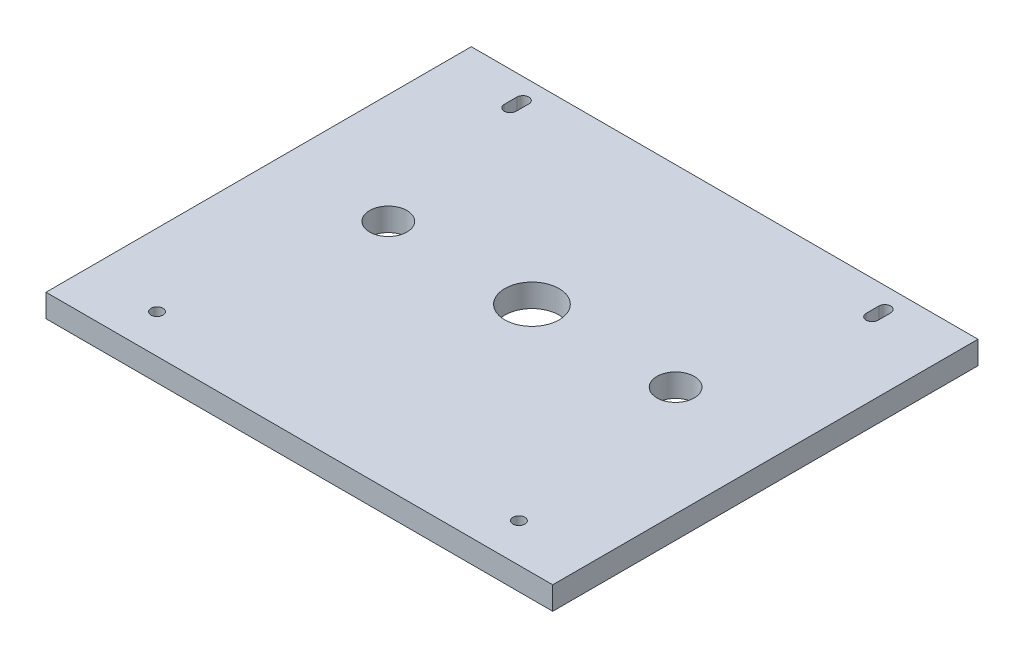
SolidWorks part; units mm, degrees
ref_plane "Front Plane" through (0, 0, 0) normal (0, 0, 1) x (1, 0, 0)
ref_plane "Top Plane" through (0, 0, 0) normal (0, 1, 0) x (1, 0, 0)
ref_plane "Right Plane" through (0, 0, 0) normal (1, 0, 0) x (0, 0, -1)
sketch "Sketch1" plane through (0, 0, 0) normal (0, 1, 0) x (1, 0, 0)
  line L1 (0, 0) -> (140, 0)
  line L2 (0, 0) -> (0, 117.505)
  line L3 (0, 117.505) -> (140, 117.505)
  line L4 (140, 0) -> (140, 117.505)
  dimension "D1" = 117.505
  dimension "D2" = 140
extrude "Boss-Extrude1" add sketch "Sketch1" along normal blind 6.35
sketch "Sketch2" plane through (0, 6.35, 0) normal (0, 1, 0) x (1, 0, 0)
  line L1 (0, 117.505) -> (0, 0) construction
  line L2 (140, 0) -> (140, 117.505) construction
  line L3 (70, 117.505) -> (70, 0) construction
  line L4 (140, 117.505) -> (0, 117.505) construction
  line L5 (0, 0) -> (140, 0) construction
  line L6 (0, 10.675) -> (140, 10.675) construction
  line L7 (0, 110.005) -> (140, 110.005) construction
  line L8 (120, 108.255) -> (120, 111.755) construction
  line L11 (20, 108.255) -> (20, 111.755) construction
  line L12 (18.35, 108.255) -> (18.35, 111.755)
  line L13 (21.65, 108.255) -> (21.65, 111.755)
  line L14 (121.65, 108.255) -> (121.65, 111.755)
  line L17 (118.35, 108.255) -> (118.35, 111.755)
  circle A0 centre (20, 10.675) radius 1.65
  arc A6 (18.35, 108.255) -> (21.65, 108.255) centre (20, 108.255) ccw
  arc A7 (21.65, 111.755) -> (18.35, 111.755) centre (20, 111.755) ccw
  circle A12 centre (70, 64.265) radius 7.5
  circle A15 centre (30.3125, 64.265) radius 5.16
  circle A16 centre (120, 10.675) radius 1.65
  circle A17 centre (109.6875, 64.265) radius 5.16
  arc A18 (121.65, 108.255) -> (118.35, 108.255) centre (120, 108.255) cw
  arc A19 (118.35, 111.755) -> (121.65, 111.755) centre (120, 111.755) cw
  point P26 (120, 110.005)
  point P33 (20, 110.005)
  dimension "D5" = 3.3
  dimension "D10" = 15
  dimension "D8" = 10.32
  dimension "D2" = 45.74
  dimension "D3" = 50
  dimension "D4" = 50
  dimension "D6" = 3.3
  dimension "D7" = 3.5
  dimension "D9" = 39.6875
  dimension "D11" = 10.675
  dimension "D13" = 53.59
extrude "Cut-Extrude1" cut sketch "Sketch2" against normal through all
